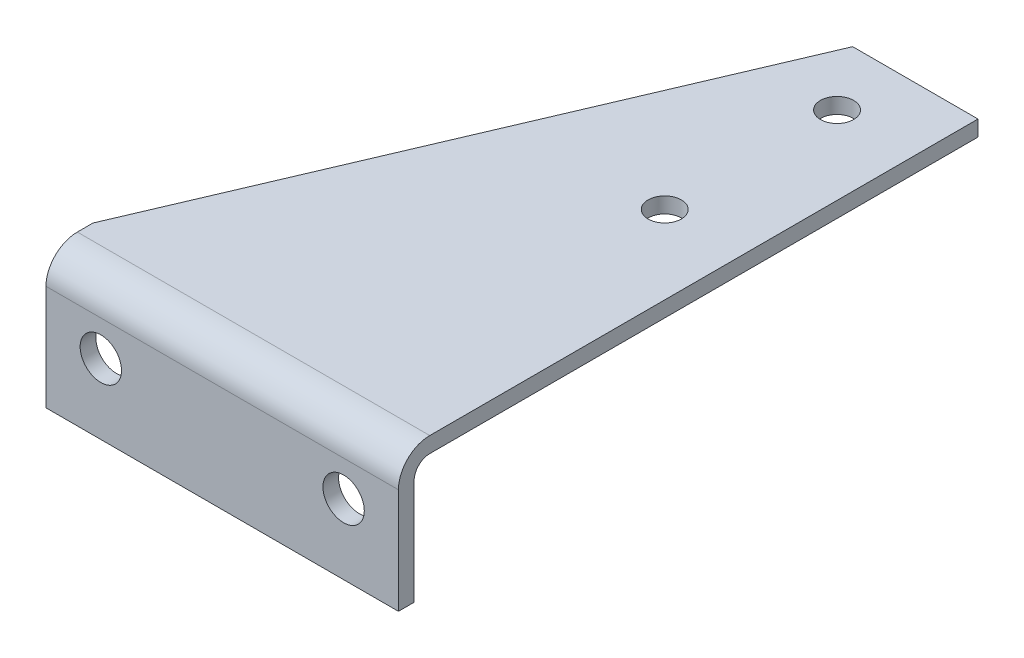
SolidWorks part; units mm, degrees
material "ASTM A36"
ref_plane "Front" through (0, 0, 0) normal (0, 0, 1) x (1, 0, 0)
ref_plane "Top" through (0, 0, 0) normal (0, 1, 0) x (1, 0, 0)
ref_plane "Side" through (0, 0, 0) normal (1, 0, 0) x (0, 0, -1)
sketch "Sketch1" plane through (0, 0, 0) normal (1, 0, 0) x (0, 0, -1)
  line L0 (0, 0) -> (-222.25, 0)
  line L1 (-234.95, -12.7) -> (-234.95, -55.372)
  line L2 (-234.95, -55.372) -> (-228.6, -55.372)
  line L3 (-228.6, -55.372) -> (-228.6, -12.7)
  line L4 (-222.25, -6.35) -> (0, -6.35)
  line L5 (0, -6.35) -> (0, 0)
  arc A0 (-228.6, -12.7) -> (-222.25, -6.35) centre (-222.25, -12.7) cw
  arc A1 (-234.95, -12.7) -> (-222.25, 0) centre (-222.25, -12.7) cw
  dimension "D5" = 6.35
  dimension "D6" = 12.7
  dimension "D1" = 6.35
  dimension "D2" = 228.6
  dimension "D3" = 6.35
  dimension "D4" = 49.022
extrude "Base-Extrude" add sketch "Sketch1" against normal blind 142.875
sketch "Sketch2" plane through (0, 0, 234.95) normal (0, 0, 1) x (1, 0, 0)
  line L0 (-142.875, -12.7) -> (-142.875, -55.372) construction
  line L1 (-142.875, -6.35) -> (0, -6.35) construction
  circle A0 centre (-120.65, -26.9875) radius 8.382
  circle A1 centre (-22.225, -26.9875) radius 8.382
  dimension "D1" = 16.764
  dimension "D4" = 20.6375
  dimension "D2" = 22.225
  dimension "D3" = 98.425
extrude "Cut-Extrude1" cut sketch "Sketch2" against normal up to next
sketch "Sketch3" plane through (0, 0, 0) normal (0, 1, 0) x (-1, 0, 0)
  line L0 (142.875, 215.9) -> (50.8, 0)
  line L1 (142.875, 0) -> (142.875, 222.25) construction
  line L3 (142.875, 234.95) -> (0, 234.95) construction
  line L4 (142.875, 0) -> (0, 0) construction
  line L5 (142.875, 0) -> (142.875, 215.9)
  line L6 (142.875, 0) -> (50.8, 0)
  line L8 (142.875, 0) -> (0, 0) construction
  line L11 (0, 0) -> (0, 222.25) construction
  circle A0 centre (31.75, 95.25) radius 6.731
  circle A1 centre (31.75, 25.4) radius 6.731
  dimension "D3" = 13.462
  dimension "D4" = 139.7
  dimension "D5" = 69.85
  dimension "D6" = 31.75
  dimension "D1" = 19.05
  dimension "D2" = 50.8
extrude "Cut-Extrude2" cut sketch "Sketch3" against normal up to next
mirror "Mirror All1" [suppressed]
sketch "Sketch6" [suppressed] plane through (0, 0, 234.95) normal (0, 0, 1) x (1, 0, 0)
  line L0 (-142.875, -12.7) -> (-142.875, -98.044) construction
  line L1 (-142.875, -55.372) -> (2.3185, -55.372)
  line L2 (-142.875, -55.372) -> (-142.875, 3.8161)
  line L3 (-142.875, 3.8161) -> (2.3185, 3.8161)
  line L4 (2.3185, -55.372) -> (2.3185, 3.8161)
  dimension "D1" = 59.1881
  dimension "D2" = 145.1935
extrude "Cut-Extrude3" [suppressed] cut sketch "Sketch6" against normal blind 188.214
